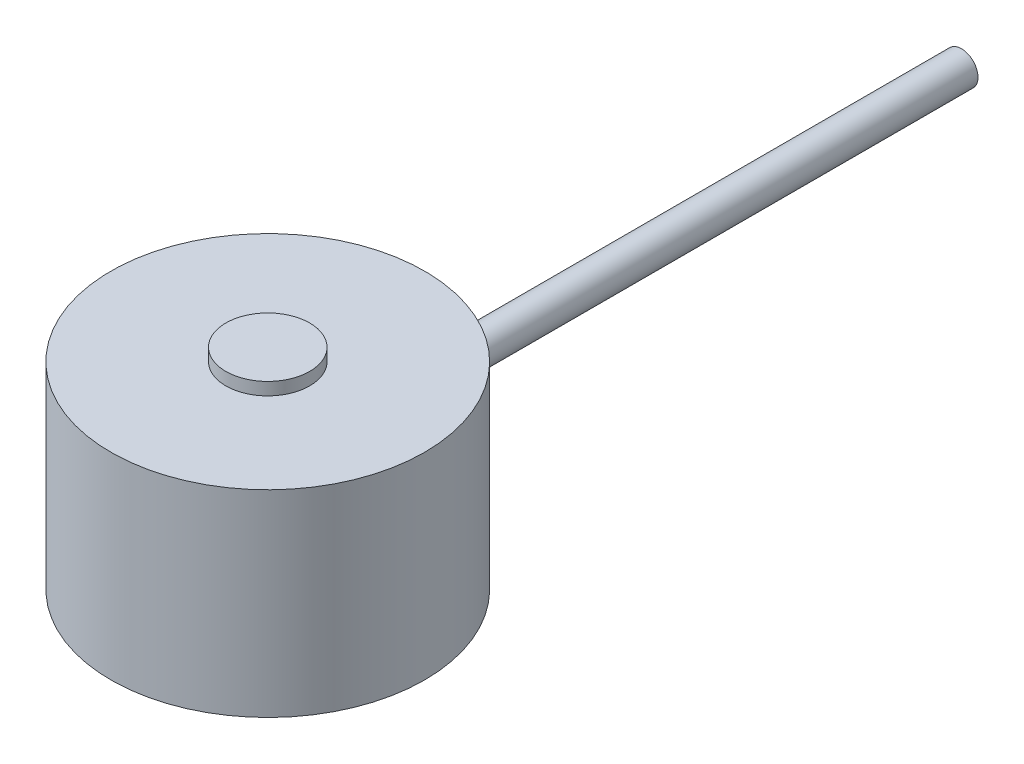
SolidWorks part; units mm, degrees
ref_plane "Front Plane" through (0, 0, 0) normal (0, 0, 1) x (1, 0, 0)
ref_plane "Top Plane" through (0, 0, 0) normal (0, 1, 0) x (1, 0, 0)
ref_plane "Right Plane" through (0, 0, 0) normal (1, 0, 0) x (0, 0, -1)
sketch "Sketch2" plane through (0, 0, 0) normal (0, 0, 1) x (1, 0, 0)
  line L0 (0, 0) -> (0, 12.7)
  line L2 (9.5, 11.94) -> (9.5, 0)
  line L3 (9.5, 0) -> (0, 0)
  line L4 (2.54, 12.7) -> (2.54, 11.94)
  line L5 (2.54, 11.94) -> (9.5, 11.94)
  line L6 (0, 12.7) -> (2.54, 12.7)
  dimension "D1" = 12.7
  dimension "D2" = 0.76
  dimension "D3" = 9.5
  dimension "D4" = 2.54
revolve "Revolve1" add sketch "Sketch2" angle 360 about L0
sketch "Sketch3" plane through (0, 0, 0) normal (0, 0, 1) x (1, 0, 0)
  circle A0 centre (0, 6.35) radius 1
  dimension "D2" = 2
  dimension "D1" = 6.35
extrude "Boss-Extrude1" add sketch "Sketch3" against normal blind 42
